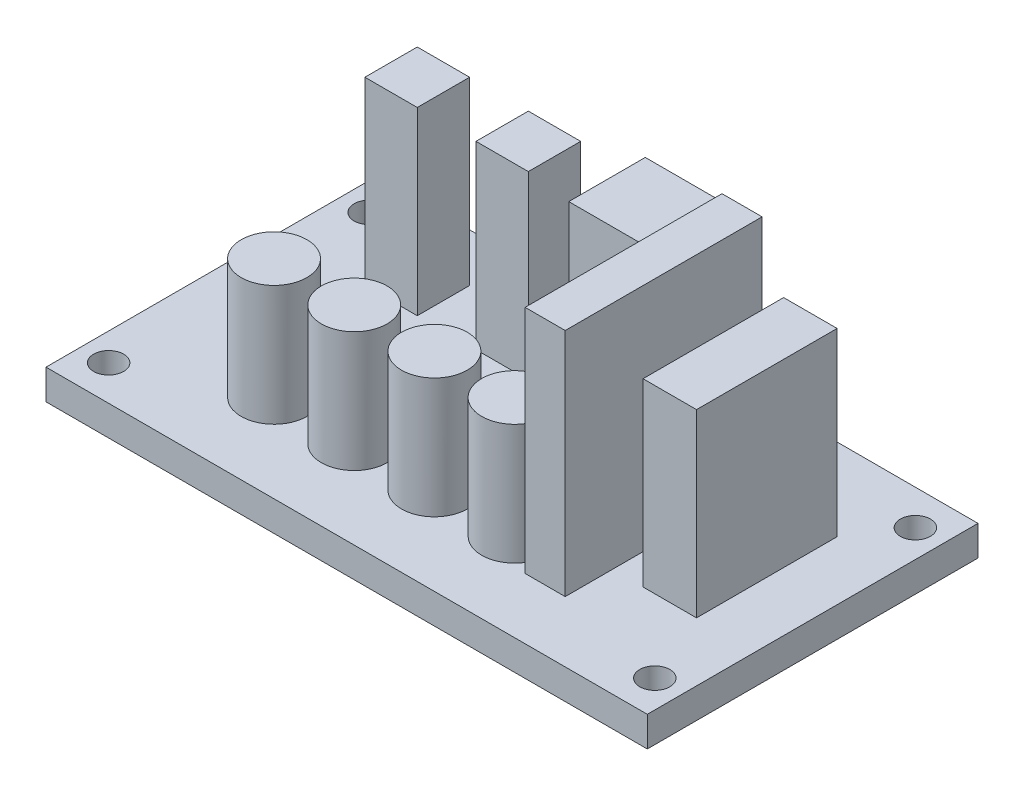
SolidWorks part; units mm, degrees
ref_plane "Face" through (0, 0, 0) normal (0, 0, 1) x (1, 0, 0)
ref_plane "Dessus" through (0, 0, 0) normal (0, 1, 0) x (1, 0, 0)
ref_plane "Droite" through (0, 0, 0) normal (1, 0, 0) x (0, 0, -1)
sketch "Esquisse1" plane through (0, 0, 0) normal (0, 1, 0) x (1, 0, 0)
  line L0 (0, 16.5) -> (60, 16.5) construction
  line L1 (0, 0) -> (60, 0)
  line L2 (0, 0) -> (0, 33)
  line L3 (0, 33) -> (60, 33)
  line L4 (60, 0) -> (60, 33)
  line L5 (30, 33) -> (30, 0) construction
  circle A0 centre (2.75, 29.5) radius 1.5
  circle A1 centre (57.25, 29.5) radius 1.5
  circle A2 centre (57.25, 3.5) radius 1.5
  circle A3 centre (2.75, 3.5) radius 1.5
  dimension "D3" = 3
  dimension "D1" = 33
  dimension "D2" = 60
  dimension "D4" = 26
  dimension "D5" = 54.5
extrude "Extrusion1" add sketch "Esquisse1" along normal blind 3
sketch "Esquisse2" plane through (0, 3, 0) normal (0, 1, 0) x (1, 0, 0)
  line L1 (29.7763, 30.0228) -> (37.4105, 30.0228)
  line L2 (29.7763, 30.0228) -> (29.7763, 22.3886)
  line L3 (29.7763, 22.3886) -> (37.4105, 22.3886)
  line L4 (37.4105, 30.0228) -> (37.4105, 22.3886)
  line L5 (48.7885, 24.8147) -> (54.1263, 24.8147)
  line L6 (48.7885, 24.8147) -> (48.7885, 10.7874)
  line L7 (48.7885, 10.7874) -> (54.1263, 10.7874)
  line L8 (54.1263, 24.8147) -> (54.1263, 10.7874)
  line L13 (8.8572, 28.1893) -> (14.0816, 28.1893)
  line L14 (8.8572, 28.1893) -> (8.8572, 22.965)
  line L15 (8.8572, 22.965) -> (14.0816, 22.965)
  line L16 (14.0816, 28.1893) -> (14.0816, 22.965)
  line L17 (19.94, 28.1893) -> (25.1643, 28.1893)
  line L18 (19.94, 28.1893) -> (19.94, 22.965)
  line L19 (19.94, 22.965) -> (25.1643, 22.965)
  line L20 (25.1643, 28.1893) -> (25.1643, 22.965)
extrude "Extrusion2" add sketch "Esquisse2" along normal blind 18
sketch "Esquisse3" plane through (0, 3, 0) normal (0, 1, 0) x (1, 0, 0)
  line L0 (0, 8.7568) -> (60, 8.7568) construction
  line L1 (0, 33) -> (0, 0) construction
  line L2 (60, 0) -> (60, 33) construction
  circle A0 centre (14, 8.7568) radius 3.2791
  circle A1 centre (22, 8.7568) radius 3.2791
  circle A2 centre (30, 8.7568) radius 3.2791
  circle A3 centre (38, 8.7568) radius 3.2791
  dimension "D1" = 8
  dimension "D2" = 8
  dimension "D3" = 8
extrude "Extrusion3" add sketch "Esquisse3" along normal blind 12
sketch "Esquisse4" plane through (0, 3, 0) normal (0, 1, 0) x (1, 0, 0)
  line L1 (41.7375, 25.7183) -> (45.7375, 25.7183)
  line L2 (41.7375, 25.7183) -> (41.7375, 6.0722)
  line L3 (41.7375, 6.0722) -> (45.7375, 6.0722)
  line L4 (45.7375, 25.7183) -> (45.7375, 6.0722)
  dimension "D1" = 4
extrude "Extrusion4" add sketch "Esquisse4" along normal blind 23
